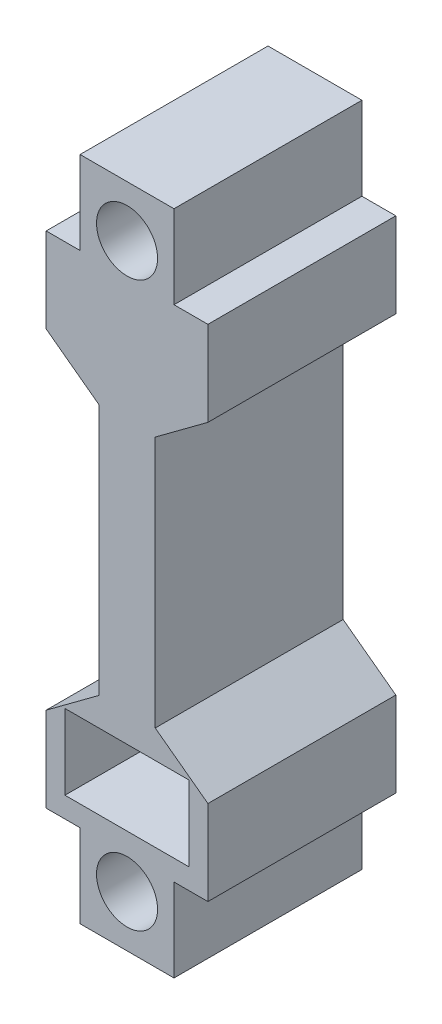
SolidWorks part; units mm, degrees
ref_plane "Front Plane" through (0, 0, 0) normal (0, 0, 1) x (1, 0, 0)
ref_plane "Top Plane" through (0, 0, 0) normal (0, 1, 0) x (1, 0, 0)
ref_plane "Right Plane" through (0, 0, 0) normal (1, 0, 0) x (0, 0, -1)
sketch "Sketch1" plane through (0, 0, 0) normal (0, 0, 1) x (1, 0, 0)
  line L0 (0, 40.6825) -> (0, -27.427) construction
  line L5 (-8.6071, 26.6028) -> (-4.9981, 26.6028)
  line L6 (-8.6071, 26.6028) -> (-8.6071, 17.567)
  line L8 (-3, 13.4084) -> (-3, -13.4084)
  line L12 (-4.9981, 26.6028) -> (-4.9981, 35.452)
  line L13 (-4.9981, 35.452) -> (4.9981, 35.452)
  line L14 (4.9981, 26.6028) -> (4.9981, 35.452)
  line L16 (3, 13.4084) -> (3, -13.4084)
  line L18 (8.6071, 26.6028) -> (8.6071, 17.567)
  line L19 (8.6071, 26.6028) -> (4.9981, 26.6028)
  line L20 (-28.5946, 0) -> (38.3015, 0) construction
  line L21 (8.6071, -26.6028) -> (4.9981, -26.6028)
  line L22 (8.6071, -26.6028) -> (8.6071, -17.567)
  line L23 (8.6071, -17.567) -> (3, -13.4084)
  line L24 (6.6071, -24.4084) -> (6.6071, -16.4084)
  line L25 (4.9981, -26.6028) -> (4.9981, -35.452)
  line L26 (-4.9981, -35.452) -> (4.9981, -35.452)
  line L27 (-4.9981, -26.6028) -> (-4.9981, -35.452)
  line L28 (-6.6071, -16.4084) -> (6.6071, -16.4084)
  line L29 (-6.6071, -24.4084) -> (-6.6071, -16.4084)
  line L30 (6.6071, -24.4084) -> (-6.6071, -24.4084)
  line L31 (-8.6071, -17.567) -> (-3, -13.4084)
  line L32 (-8.6071, -26.6028) -> (-8.6071, -17.567)
  line L33 (-8.6071, -26.6028) -> (-4.9981, -26.6028)
  line L34 (-8.6071, 17.567) -> (-3, 13.4084)
  line L35 (8.6071, 17.567) -> (3, 13.4084)
  circle A0 centre (0, 30) radius 3.25
  circle A1 centre (0, -30) radius 3.25
  point P18 (0, 35.452)
  point P20 (0, 16.4084)
  point P21 (0, 24.4084)
  point P28 (0, -24.4084)
  point P29 (0, -16.4084)
  point P30 (0, -35.452)
  point P35 (3, 0)
  point P43 (-3, 0)
  dimension "D6" = 6.5
  dimension "D1" = 6
  dimension "D5" = 30
extrude "Boss-Extrude1" add sketch "Sketch1" along normal blind 20
